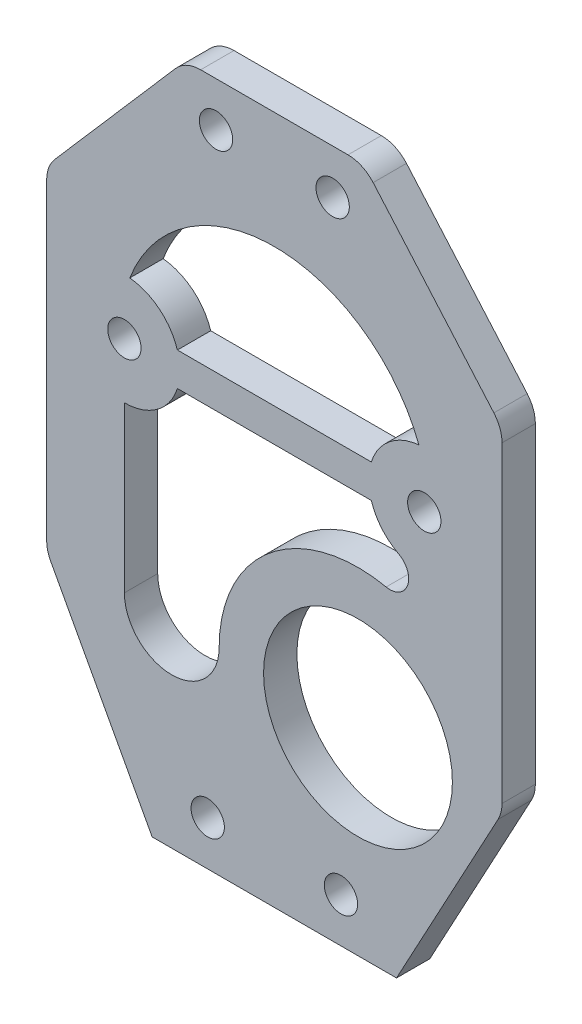
SolidWorks part; units mm, degrees
material "Galvanized Steel"
ref_plane "Front Plane" through (0, 0, 0) normal (0, 0, 1) x (1, 0, 0)
ref_plane "Top Plane" through (0, 0, 0) normal (0, 1, 0) x (1, 0, 0)
ref_plane "Right Plane" through (0, 0, 0) normal (1, 0, 0) x (0, 0, -1)
sketch "Sketch1" plane through (0, 0, 0) normal (0, 0, 1) x (1, 0, 0)
  line L0 (0, 19.3981) -> (0, -43.138) construction
  line L1 (8, 24.4003) -> (-8, 24.4003)
  line L2 (-8, 24.4003) -> (-20.5, 10)
  line L3 (-20.5, 10) -> (-20.5, -20)
  line L4 (-20.5, -20) -> (-11, -37.5997)
  line L5 (-11, -37.5997) -> (11, -37.5997)
  line L6 (20.5, -20) -> (11, -37.5997)
  line L7 (20.5, 10) -> (20.5, -20)
  line L8 (8, 24.4003) -> (20.5, 10)
  line L9 (-13.5, -5) -> (-13.5, -19.8174)
  line L13 (8.5, 0) -> (8.7303, 0) construction
  line L14 (-8.7303, 1.5) -> (8.7303, 1.5)
  line L16 (-8.7303, -1.5) -> (8.7303, -1.5)
  line L18 (0, -1.5) -> (0, 1.5) construction
  line L19 (-8.7303, 0) -> (0, 0) construction
  line L20 (-8.7303, 1.5) -> (-8.7303, -1.5) construction
  line L21 (7.5302, -19.8174) -> (17.65, -25.2799) construction
  circle A0 centre (-5.25, 20.3945) radius 1.5
  circle A1 centre (-13.5, 0) radius 1.5
  circle A2 centre (-6, -33.5997) radius 1.5
  circle A3 centre (6, -33.5997) radius 1.5
  circle A4 centre (13.5, 0) radius 1.5
  circle A5 centre (5.25, 20.3945) radius 1.5
  arc A6 (-13.5, -19.8174) -> (-4.9698, -19.8174) centre (-9.2349, -19.8174) ccw
  arc A7 (-4.9698, -19.8174) -> (10.0668, -7.5775) centre (7.5302, -19.8174) cw
  circle A11 centre (7.5302, -19.8174) radius 8.5
  arc A13 (13.0147, 4.9764) -> (-13.0147, 4.9764) centre (0, 0) ccw
  arc A15 (-13.0147, 4.9764) -> (-8.7303, 1.5) centre (-13.5, 0) cw
  arc A16 (13.0147, 4.9764) -> (8.7303, 1.5) centre (13.5, 0) ccw
  arc A17 (-8.7303, -1.5) -> (-13.5, -5) centre (-13.5, 0) cw
  arc A18 (8.7303, -1.5) -> (11.188, -4.4333) centre (13.5, 0) ccw
  arc A19 (10.0668, -7.5775) -> (11.188, -4.4333) centre (10.4088, -5.9275) ccw
  point P9 (0, -37.5997)
  point P33 (0, 0)
  dimension "D1" = 10
  dimension "D7" = 3
  dimension "D14" = 17
  dimension "D17" = 13.9337
  dimension "D19" = 3
  dimension "D18" = 5
  dimension "D20" = 45
  dimension "D21" = 4
  dimension "D2" = 16
  dimension "D3" = 10.5
  dimension "D4" = 30
  dimension "D5" = 22
  dimension "D6" = 12
  dimension "D8" = 62
  dimension "D9" = 41
  dimension "D10" = 20
  dimension "D11" = 22
  dimension "D12" = 13.5
  dimension "D13" = 4
  dimension "D15" = 11.5
  dimension "D16" = 6
extrude "Boss-Extrude1" add sketch "Sketch1" along normal mid plane 3
fillet "Fillet1" radius 3 6 edges at (-20.5, -20, 0) (20.5, -20, 0) (20.5, 10, 0) (8, 24.4003, 0) (-20.5, 10, 0) (-8, 24.4003, 0)
